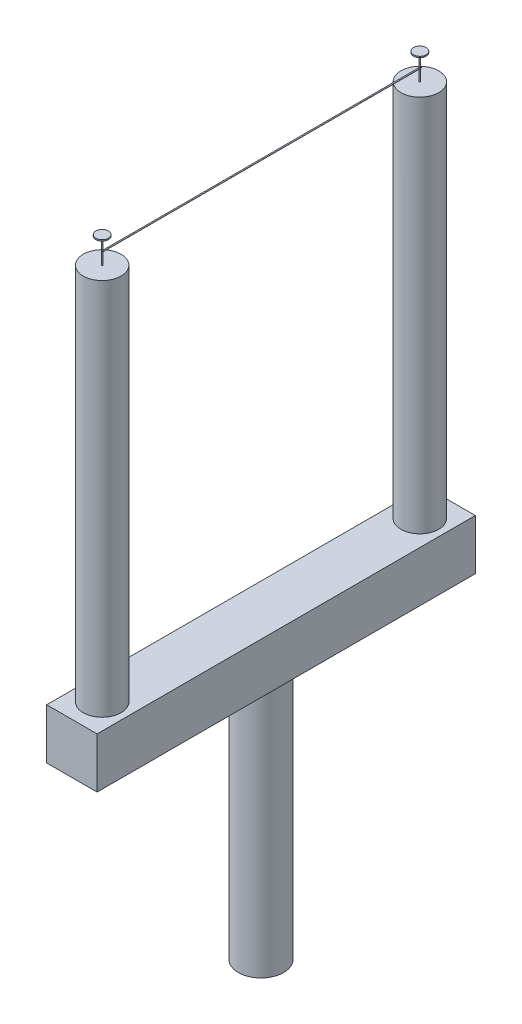
SolidWorks part; units mm, degrees
ref_plane "Front Plane" through (0, 0, 0) normal (0, 0, 1) x (1, 0, 0)
ref_plane "Top Plane" through (0, 0, 0) normal (0, 1, 0) x (1, 0, 0)
ref_plane "Right Plane" through (0, 0, 0) normal (1, 0, 0) x (0, 0, -1)
sketch "Sketch1" plane through (0, 0, 0) normal (0, 0, 1) x (1, 0, 0)
  line L1 (-10, -10) -> (10, -10)
  line L2 (-10, -10) -> (-10, 10)
  line L3 (-10, 10) -> (10, 10)
  line L4 (10, -10) -> (10, 10)
  line L5 (-10, -10) -> (10, 10) construction
  line L6 (-10, 10) -> (10, -10) construction
  point P0 (0, 0)
  dimension "D1" = 20
  dimension "D2" = 20
extrude "Boss-Extrude1" add sketch "Sketch1" along normal blind 150
sketch "Sketch2" plane through (0, 10, 0) normal (0, 1, 0) x (1, 0, 0)
  line L0 (10, -150) -> (-10, -150) construction
  circle A0 centre (0, -12) radius 7.5
  circle A1 centre (0, -138) radius 7.5
  point P7 (0, -150)
  dimension "D1" = 15
  dimension "D3" = 15
  dimension "D2" = 12
  dimension "D4" = 12
sketch "Sketch3" plane through (0, -10, 0) normal (0, -1, 0) x (1, 0, 0)
  line L0 (-10, 150) -> (10, 150) construction
  circle A0 centre (0, 75) radius 9
  point P4 (0, 150)
  dimension "D1" = 18
  dimension "D2" = 75
extrude "Boss-Extrude2" add sketch "Sketch3" along normal blind 100
extrude "Boss-Extrude3" add sketch "Sketch2" along normal blind 150
sketch "Sketch7" plane through (0, 160, 0) normal (0, 1, 0) x (1, 0, 0)
  circle A0 centre (0, -12) radius 0.25
  circle A1 centre (0, -138) radius 0.25
  dimension "D1" = 0.5
  dimension "D2" = 0.5
extrude "Boss-Extrude4" add sketch "Sketch7" along normal blind 10
sketch "Sketch8" plane through (0, 170, 0) normal (0, 1, 0) x (1, 0, 0)
  circle A0 centre (0, -12) radius 2.5
  circle A1 centre (0, -138) radius 2.5
  dimension "D1" = 5
  dimension "D2" = 5
extrude "Boss-Extrude5" add sketch "Sketch8" along normal blind 0.5
sketch "Sketch19" plane through (0, 0, 0) normal (1, 0, 0) x (0, 0, -1)
  line L0 (-11.75, 160) -> (-11.75, 170) construction
  line L1 (-11.75, 165) -> (-138.25, 165)
  line L2 (-11.75, 165) -> (-11.75, 164.9)
  line L3 (-11.75, 164.9) -> (-138.25, 164.9)
  line L4 (-138.25, 165) -> (-138.25, 164.9)
  line L5 (-138.25, 170) -> (-138.25, 160) construction
  dimension "D1" = 0.1
extrude "Boss-Extrude6" add sketch "Sketch19" along normal blind 0.5
